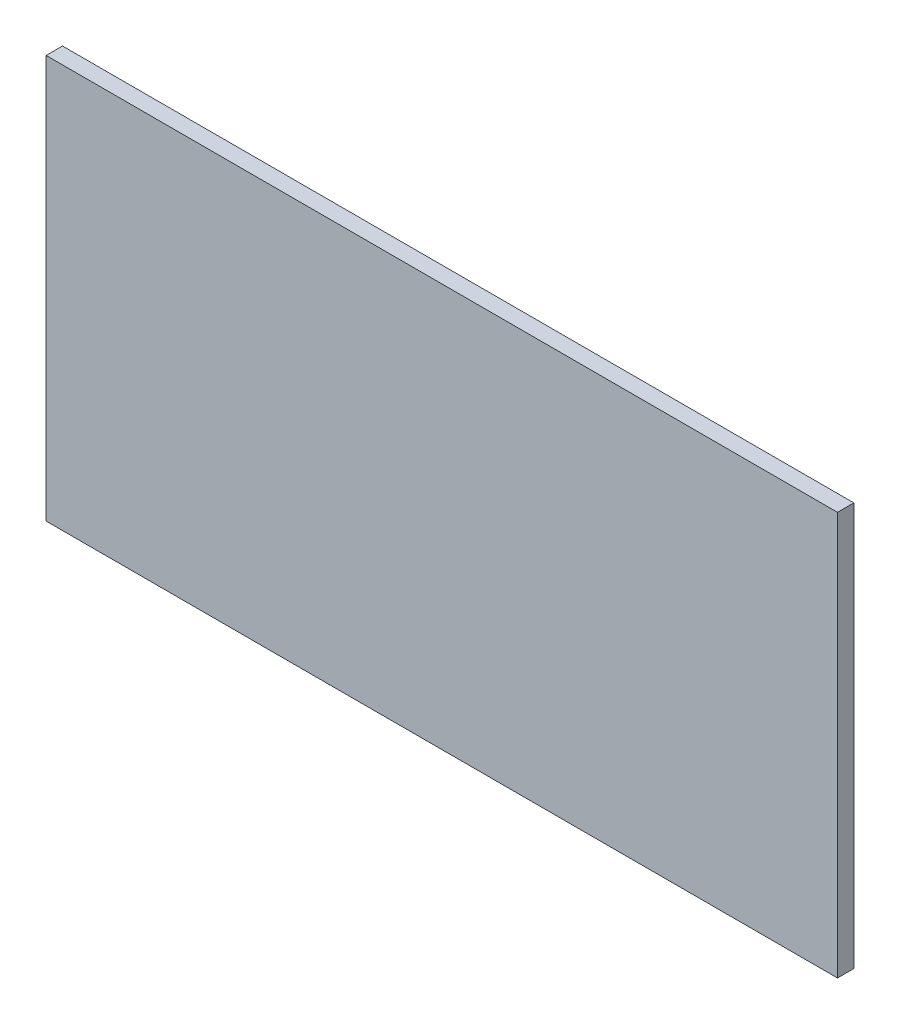
SolidWorks part; units mm, degrees
material "Pine"
ref_plane "Front Plane" through (0, 0, 0) normal (0, 0, 1) x (1, 0, 0)
ref_plane "Top Plane" through (0, 0, 0) normal (0, 1, 0) x (1, 0, 0)
ref_plane "Right Plane" through (0, 0, 0) normal (1, 0, 0) x (0, 0, -1)
sketch "Sketch1" plane through (0, 0, 0) normal (0, 0, 1) x (1, 0, 0)
  line L1 (-206.0634, 77.0973) -> (370.1991, 77.0973)
  line L2 (-206.0634, 77.0973) -> (-206.0634, -216.5902)
  line L3 (-206.0634, -216.5902) -> (370.1991, -216.5902)
  line L4 (370.1991, 77.0973) -> (370.1991, -216.5902)
  dimension "D1" = 576.2625
  dimension "D2" = 293.6875
extrude "Boss-Extrude1" add sketch "Sketch1" along normal blind 11.9062
